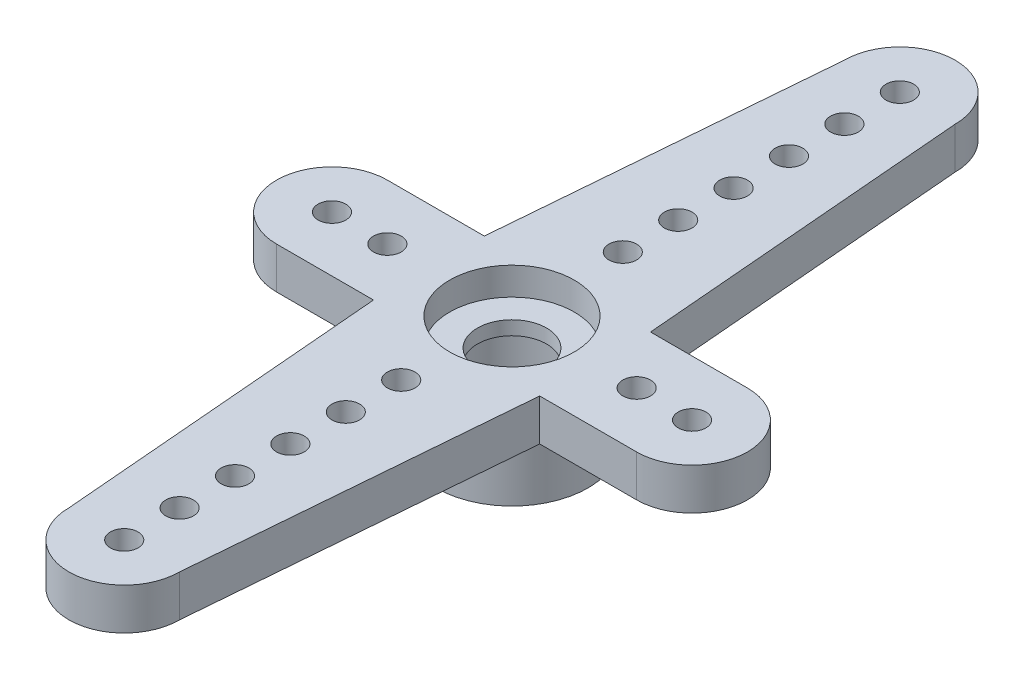
SolidWorks part; units mm, degrees
ref_plane "Plan de face" through (0, 0, 0) normal (0, 0, 1) x (1, 0, 0)
ref_plane "Plan de dessus" through (0, 0, 0) normal (0, 1, 0) x (1, 0, 0)
ref_plane "Plan de droite" through (0, 0, 0) normal (1, 0, 0) x (0, 0, -1)
sketch "Esquisse1" plane through (0, 0, 0) normal (0, 1, 0) x (1, 0, 0)
  circle A0 centre (0, 0) radius 2.25
  circle A1 centre (0, 0) radius 2.75
  dimension "D1" = 4.5
  dimension "D2" = 5.5
extrude "Boss.-Extru.1" add sketch "Esquisse1" along normal blind 2.5
sketch "Esquisse3" plane through (0, 2.5, 0) normal (0, 1, 0) x (1, 0, 0)
  line L0 (-1000, 0) -> (49000, 0) construction
  line L1 (0, -1000) -> (0, 49000) construction
  line L2 (-6.5, 2) -> (-3, 2)
  line L3 (-6.5, -2) -> (-3, -2)
  line L4 (-8.5, 2) -> (-8.5, -2) construction
  line L5 (8.5, 2) -> (8.5, -2) construction
  line L6 (3, 2) -> (2, 14)
  line L7 (-3, 2) -> (-2, 14)
  line L8 (-3, -2) -> (-2, -14)
  line L9 (3, -2) -> (2, -14)
  line L10 (3, 2) -> (6.5, 2)
  line L11 (3, -2) -> (6.5, -2)
  arc A0 (6.5, -2) -> (6.5, 2) centre (6.5, 0) ccw
  arc A1 (-6.5, 2) -> (-6.5, -2) centre (-6.5, 0) ccw
  arc A2 (2, 14) -> (-2, 14) centre (0, 14) ccw
  arc A3 (2, -14) -> (-2, -14) centre (0, -14) cw
  dimension "D7" = 2
  dimension "D1" = 17
  dimension "D2" = 17
  dimension "D3" = 4
  dimension "D4" = 3
  dimension "D5" = 12
  dimension "D6" = 2
extrude "Boss.-Extru.2" add sketch "Esquisse3" along normal blind 1.5
sketch "Esquisse4" plane through (0, 4, 0) normal (0, 1, 0) x (1, 0, 0)
  circle A0 centre (0, 0) radius 2.25
  dimension "D1" = 4.5
extrude "Enlèv. mat.-Extru.1" cut sketch "Esquisse4" against normal blind 1
sketch "Esquisse5" plane through (0, 3, 0) normal (0, 1, 0) x (1, 0, 0)
  circle A0 centre (0, 0) radius 1.25
  dimension "D1" = 2.5
extrude "Enlèv. mat.-Extru.2" cut sketch "Esquisse5" against normal up to next
sketch "Esquisse6" plane through (0, 4, 0) normal (0, 1, 0) x (1, 0, 0)
  line L0 (-1000, 0) -> (49000, 0) construction
  line L1 (0, -1000) -> (0, 49000) construction
  circle A0 centre (4.5, 0) radius 0.5
  circle A1 centre (0, 0) radius 2.25 construction
  circle A2 centre (6.5, 0) radius 0.5
  circle A3 centre (-4.5, 0) radius 0.5
  circle A4 centre (-6.5, 0) radius 0.5
  circle A5 centre (0, 14) radius 0.5
  arc A6 (2, 14) -> (-2, 14) centre (0, 14) ccw construction
  circle A7 centre (0, 12) radius 0.5
  circle A8 centre (0, 10) radius 0.5
  circle A9 centre (0, 8) radius 0.5
  circle A10 centre (0, 6) radius 0.5
  circle A11 centre (0, 4) radius 0.5
  circle A12 centre (0, -4) radius 0.5
  circle A13 centre (0, -6) radius 0.5
  circle A14 centre (0, -8) radius 0.5
  circle A15 centre (0, -10) radius 0.5
  circle A16 centre (0, -12) radius 0.5
  circle A17 centre (0, -14) radius 0.5
  dimension "D1" = 1
  dimension "D3" = 1
  dimension "D4" = 2
  dimension "D5" = 1
  dimension "D2" = 4.5
  dimension "D6" = 6
extrude "Enlèv. mat.-Extru.3" cut sketch "Esquisse6" against normal through all
